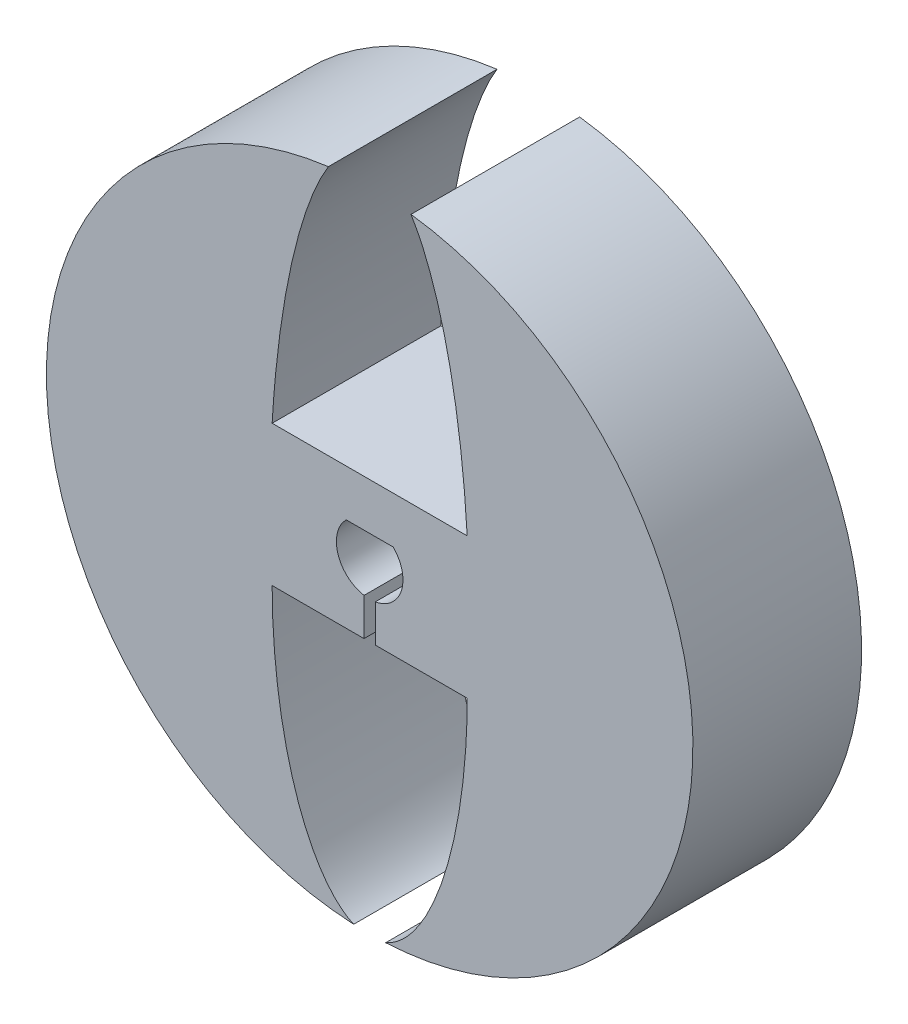
SolidWorks part; units mm, degrees
ref_plane "Front Plane" through (0, 0, 0) normal (0, 0, 1) x (1, 0, 0)
ref_plane "Top Plane" through (0, 0, 0) normal (0, 1, 0) x (1, 0, 0)
ref_plane "Right Plane" through (0, 0, 0) normal (1, 0, 0) x (0, 0, -1)
sketch "Sketch1" plane through (0, 0, 0) normal (0, 0, 1) x (1, 0, 0)
  circle A0 centre (0, 0) radius 23
  dimension "D1" = 46
extrude "Boss-Extrude1" add sketch "Sketch1" along normal blind 12
sketch "Sketch2" plane through (0, 0, 12) normal (0, 0, 1) x (1, 0, 0)
  line L0 (-2.37, 0) -> (2.37, 0) construction
  line L1 (-1.6697, 1.682) -> (1.6697, 1.682)
  line L2 (-26.1758, 0) -> (30.687, 0) construction
  line L3 (0, 5) -> (0, -26.6479) construction
  line L4 (-6.9394, 5) -> (6.9394, 5)
  line L5 (-6.9394, -5) -> (-0.4, -5)
  line L6 (-0.4, -5) -> (-0.4, -2.336)
  line L7 (0.4, -5) -> (0.4, -2.336)
  line L8 (0.4, -5) -> (6.9394, -5)
  arc A0 (-1.6697, 1.682) -> (-0.4, -2.336) centre (0, 0) ccw
  arc A1 (0.4, -2.336) -> (1.6697, 1.682) centre (0, 0) ccw
  ellipse E0 centre (0, -5) end of major axis (0, 13.218) minor radius 6.9394 (-6.9394, -5) -> (6.9394, -5) ccw
  ellipse E1 centre (0, 0) end of major axis (0, 25.0742) minor radius 7.0816 (6.9394, 5) -> (-6.9394, 5) ccw
  dimension "D1" = 4.74
  dimension "D2" = 1.682
  dimension "D3" = 0.4
extrude "Cut-Extrude1" cut sketch "Sketch2" against normal through all
